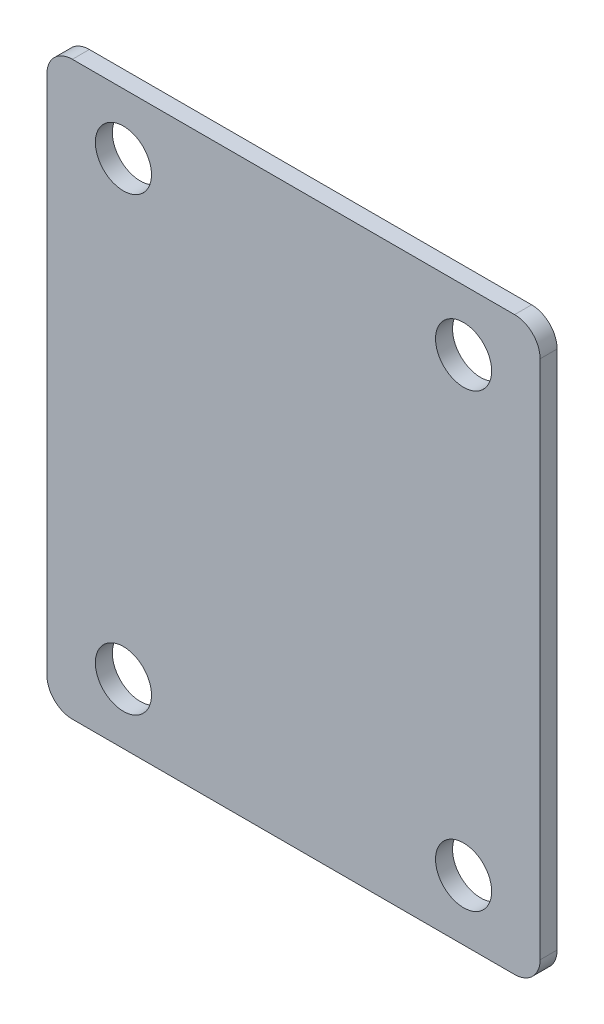
SolidWorks part; units mm, degrees
ref_plane "Front Plane" through (0, 0, 0) normal (0, 0, 1) x (1, 0, 0)
ref_plane "Top Plane" through (0, 0, 0) normal (0, 1, 0) x (1, 0, 0)
ref_plane "Right Plane" through (0, 0, 0) normal (1, 0, 0) x (0, 0, -1)
sketch "Sketch1" plane through (0, 0, 0) normal (0, 0, 1) x (1, 0, 0)
  line L1 (26, -30.6) -> (-26, -30.6)
  line L2 (26, -30.6) -> (26, 30.6)
  line L3 (26, 30.6) -> (-26, 30.6)
  line L4 (-26, -30.6) -> (-26, 30.6)
extrude "Boss-Extrude1" add sketch "Sketch1" along normal blind 2
hole_wizard "M6 Clearance Hole1" positions "Sketch2" profile "Sketch3" hole size "M6" standard "ISO" end condition through all
sketch "Sketch2" plane through (0, 0, 2) normal (0, 0, 1) x (1, 0, 0)
  point P2 (20, -26.5)
  point P5 (-20, -26.5)
  point P8 (-20, 26.5)
  point P11 (20, 26.5)
sketch "Sketch3" plane through (20, -26.5, 2) normal (1, 0, 0) x (0, -1, 0)
  line L0 (0, 0) -> (0, 2)
  line L1 (0, 2) -> (3.3, 2)
  line L2 (3.3, 2) -> (3.3, 0)
  line L5 (3.3, 0) -> (0, 0)
  line L11 (0, -6.35) -> (0, 107.95) construction
  dimension "Thru Hole Dia." = 6.6
  dimension "Thru Hole Depth" = 2
sketch "Sketch4" plane through (0, 0, 2) normal (0, 0, 1) x (1, 0, 0)
  line L1 (-26, 30.6) -> (26, 30.6)
  line L2 (-26, 30.6) -> (-26, -30.6)
  line L3 (-26, -30.6) -> (26, -30.6)
  line L4 (26, 30.6) -> (26, -30.6)
  line L5 (-26, 33.6) -> (26, 33.6)
  line L6 (-29, 30.6) -> (-29, -30.6)
  line L7 (-26, -33.6) -> (26, -33.6)
  line L8 (29, 30.6) -> (29, -30.6)
  arc A0 (-29, -30.6) -> (-26, -33.6) centre (-26, -30.6) ccw
  arc A1 (26, -33.6) -> (29, -30.6) centre (26, -30.6) ccw
  arc A2 (26, 33.6) -> (29, 30.6) centre (26, 30.6) cw
  arc A3 (-26, 33.6) -> (-29, 30.6) centre (-26, 30.6) ccw
  dimension "D5" = 3
  dimension "D1" = 3
  dimension "D2" = 3
  dimension "D3" = 3
  dimension "D4" = 3
extrude "Boss-Extrude2" add sketch "Sketch4" against normal blind 2
